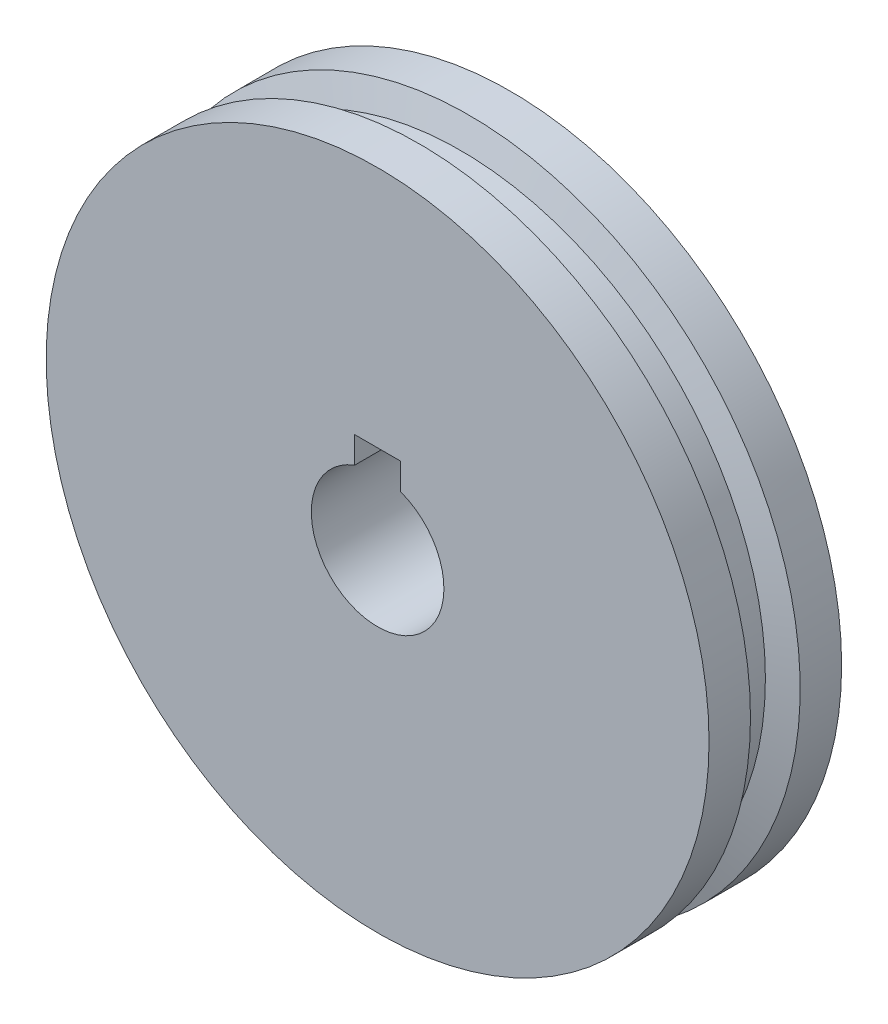
SolidWorks part; units mm, degrees
ref_plane "Front Plane" through (0, 0, 0) normal (0, 0, 1) x (1, 0, 0)
ref_plane "Top Plane" through (0, 0, 0) normal (0, 1, 0) x (1, 0, 0)
ref_plane "Right Plane" through (0, 0, 0) normal (1, 0, 0) x (0, 0, -1)
sketch "Sketch1" plane through (0, 0, 0) normal (0, 0, 1) x (1, 0, 0)
  circle A0 centre (0, 0) radius 5
  circle A1 centre (0, 0) radius 25
  dimension "D1" = 10
  dimension "D2" = 50
extrude "Boss-Extrude1" add sketch "Sketch1" along normal mid plane 10
sketch "Sketch2" plane through (0, 0, 0) normal (1, 0, 0) x (0, 0, -1)
  line L0 (-2.5, 27) -> (-1.25, 23)
  line L1 (-1.25, 23) -> (1.25, 23)
  line L2 (1.25, 23) -> (2.5, 27)
  line L3 (2.5, 27) -> (-2.5, 27)
  line L4 (-14.2374, 0) -> (10.1614, 0) construction
  point P2 (0, 23)
  dimension "D1" = 2.5
  dimension "D2" = 5
  dimension "D3" = 4
  dimension "D4" = 23
revolve "Cut-Revolve1" cut sketch "Sketch2" angle 360 about L4
sketch "Sketch3" plane through (0, 0, -5) normal (0, 0, -1) x (-1, 0, 0)
  line L0 (-1.7329, 6.6901) -> (1.7329, 6.6901)
  line L1 (1.7329, 6.6901) -> (1.7329, 4.6901)
  line L3 (-1.7329, 6.6901) -> (-1.7329, 4.6901)
  circle A0 centre (0, 0) radius 5 construction
  arc A1 (-1.7329, 4.6901) -> (1.7329, 4.6901) centre (0, 0) cw
  point P0 (0, 6.6901)
  dimension "D1" = 2
extrude "Cut-Extrude1" cut sketch "Sketch3" against normal blind 10
